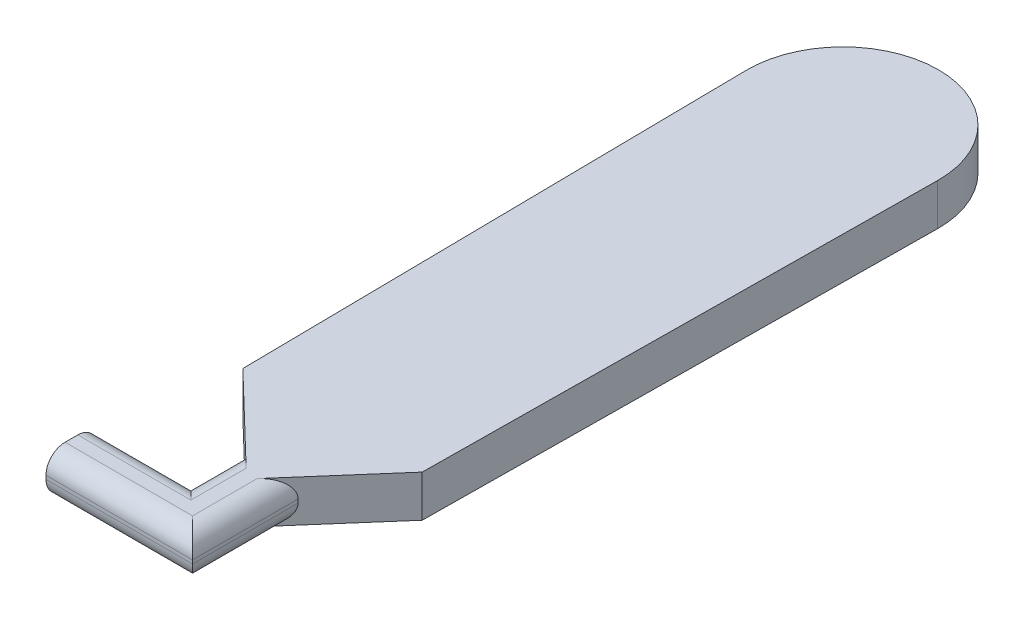
SolidWorks part; units mm, degrees
ref_plane "Front Plane" through (0, 0, 0) normal (0, 0, 1) x (1, 0, 0)
ref_plane "Top Plane" through (0, 0, 0) normal (0, 1, 0) x (1, 0, 0)
ref_plane "Right Plane" through (0, 0, 0) normal (1, 0, 0) x (0, 0, -1)
sketch "Sketch2" plane through (0, 0, 0) normal (0, 1, 0) x (1, 0, 0)
  line L0 (-4.4522, 98.0892) -> (96.0743, 98.0892) construction
  line L1 (7.673, 77.7507) -> (6.0346, 204.9371)
  line L2 (51.9756, 204.9371) -> (50.6772, 77.7507)
  line L3 (7.673, 77.7507) -> (24.1924, 61.8552)
  line L4 (24.1924, 61.8552) -> (36.8166, 61.8552)
  line L5 (36.8166, 61.8552) -> (50.6772, 77.7507)
  line L6 (24.1924, 61.8552) -> (24.1924, 48.7663)
  line L7 (24.1924, 48.7663) -> (1.6729, 48.7663)
  line L8 (1.6729, 48.7663) -> (1.6729, 36.5646)
  line L9 (1.6729, 36.5646) -> (36.8166, 36.5646)
  line L10 (36.8166, 36.5646) -> (36.8166, 61.8552)
  circle A0 centre (29.0117, 200.2428) radius 22.9148
  point P8 (0, 0)
  point P14 (0, 0)
extrude "Boss-Extrude1" add sketch "Sketch2" along normal blind 10 contours L1 L0 L2 A0 | A0 | L0 L1 L3 L4 L5 L2 | L9 L10 L4 L6 L7 L8
fillet "Fillet1" radius 4.572 8 edges at (19.2448, 0, -36.5646) (19.2448, 10, -36.5646) (36.8166, 0, -49.2099) (36.8166, 10, -49.2099) (24.1924, 0, -55.3108) (24.1924, 10, -55.3108) (12.9327, 0, -48.7663) (12.9327, 10, -48.7663)
